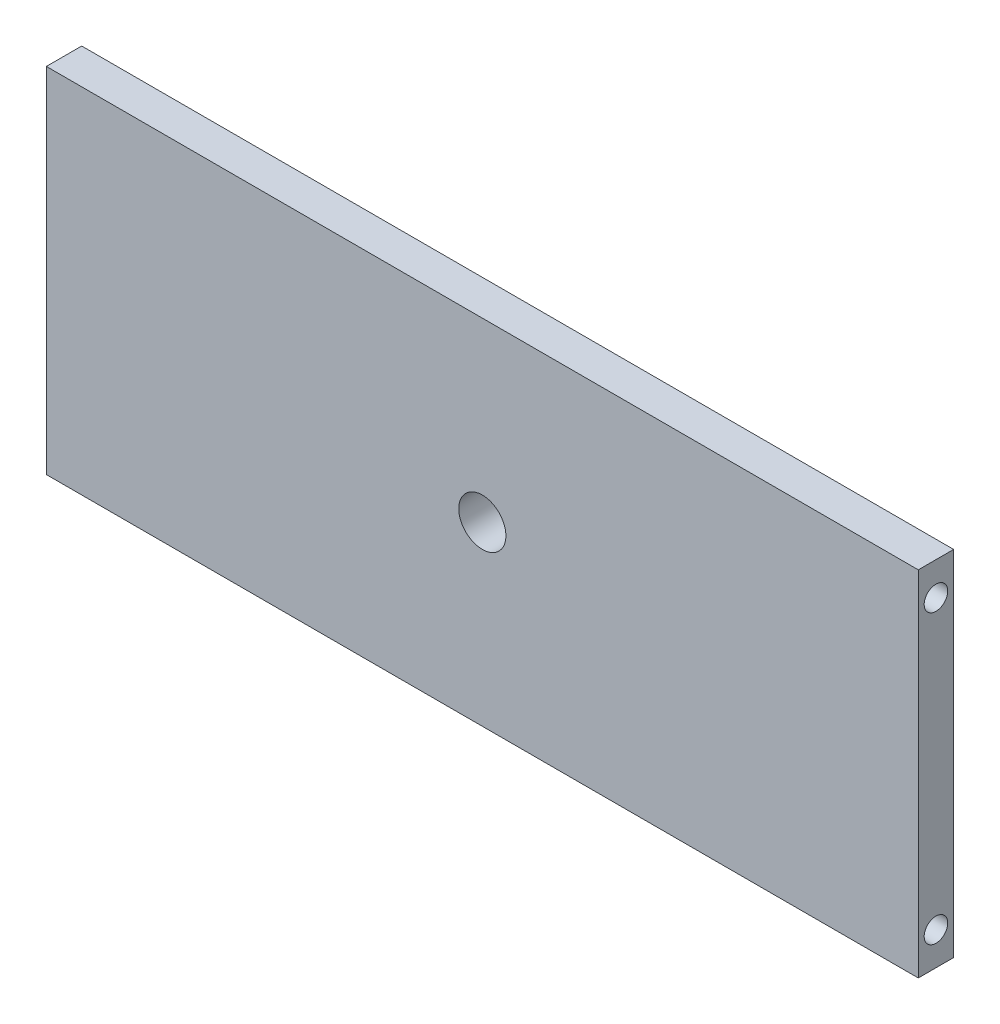
SolidWorks part; units mm, degrees
ref_plane "Front Plane" through (0, 0, 0) normal (0, 0, 1) x (1, 0, 0)
ref_plane "Top Plane" through (0, 0, 0) normal (0, 1, 0) x (1, 0, 0)
ref_plane "Right Plane" through (0, 0, 0) normal (1, 0, 0) x (0, 0, -1)
sketch "Sketch1" plane through (0, 0, 0) normal (0, 0, 1) x (1, 0, 0)
  line L1 (-185, 75) -> (185, 75)
  line L2 (-185, 75) -> (-185, -75)
  line L3 (-185, -75) -> (185, -75)
  line L4 (185, 75) -> (185, -75)
  line L5 (-185, 75) -> (185, -75) construction
  line L6 (-185, -75) -> (185, 75) construction
  point P0 (0, 0)
  dimension "D1" = 370
  dimension "D2" = 150
extrude "Boss-Extrude1" add sketch "Sketch1" along normal blind 15
sketch "Sketch2" plane through (-185, 0, 0) normal (-1, 0, 0) x (0, 0, 1)
  line L0 (7.5, 93.0951) -> (7.5, -89.2482) construction
  line L1 (15, 75) -> (0, 75) construction
  line L2 (15, -75) -> (0, -75) construction
  circle A0 centre (7.5, 61) radius 5
  circle A1 centre (7.5, -61) radius 5
  dimension "D1" = 10
  dimension "D2" = 7.5
  dimension "D3" = 14
  dimension "D4" = 14
extrude "Cut-Extrude1" cut sketch "Sketch2" against normal blind 30
sketch "Sketch3" plane through (185, 0, 0) normal (1, 0, 0) x (0, 0, -1)
  line L0 (-7.5, 89.5559) -> (-7.5, -94.6338) construction
  line L1 (-15, 75) -> (0, 75) construction
  line L2 (-15, -75) -> (0, -75) construction
  circle A0 centre (-7.5, 61) radius 5
  circle A1 centre (-7.5, -61) radius 5
  dimension "D2" = 10
  dimension "D1" = 7.5
  dimension "D3" = 14
  dimension "D4" = 14
extrude "Cut-Extrude2" cut sketch "Sketch3" against normal blind 30
sketch "Sketch4" plane through (0, 0, 15) normal (0, 0, 1) x (1, 0, 0)
  circle A0 centre (0, 0) radius 10
  dimension "D1" = 20
extrude "Cut-Extrude3" cut sketch "Sketch4" against normal through all
